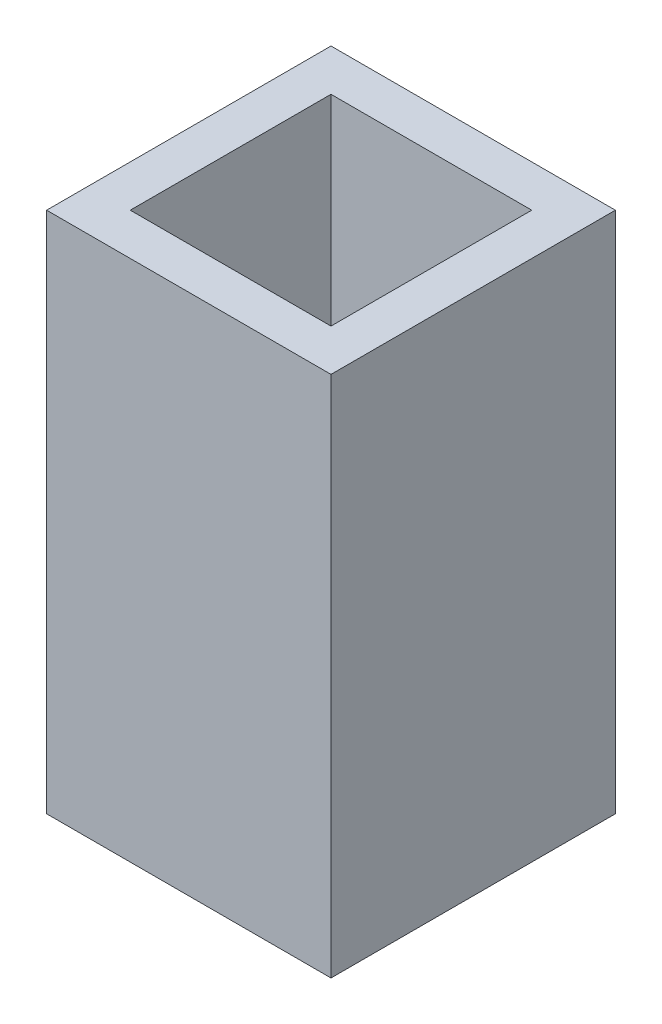
SolidWorks part; units mm, degrees
ref_plane "Front Plane" through (0, 0, 0) normal (0, 0, 1) x (1, 0, 0)
ref_plane "Top Plane" through (0, 0, 0) normal (0, 1, 0) x (1, 0, 0)
ref_plane "Right Plane" through (0, 0, 0) normal (1, 0, 0) x (0, 0, -1)
sketch "Sketch1" plane through (0, 0, 0) normal (0, 1, 0) x (1, 0, 0)
  line L1 (-4.8, -4.8) -> (4.8, -4.8)
  line L2 (-4.8, -4.8) -> (-4.8, 4.8)
  line L3 (-4.8, 4.8) -> (4.8, 4.8)
  line L4 (4.8, -4.8) -> (4.8, 4.8)
  line L5 (-4.8, -4.8) -> (4.8, 4.8) construction
  line L6 (-4.8, 4.8) -> (4.8, -4.8) construction
  line L7 (-6.8, -6.8) -> (6.8, -6.8)
  line L8 (-6.8, -6.8) -> (-6.8, 6.8)
  line L9 (-6.8, 6.8) -> (6.8, 6.8)
  line L10 (6.8, -6.8) -> (6.8, 6.8)
  line L11 (-6.8, -6.8) -> (6.8, 6.8) construction
  line L12 (-6.8, 6.8) -> (6.8, -6.8) construction
  point P0 (0, 0)
  point P6 (0, 0)
  dimension "D1" = 9.6
  dimension "D2" = 13.6
extrude "Boss-Extrude1" add sketch "Sketch1" along normal blind 25
